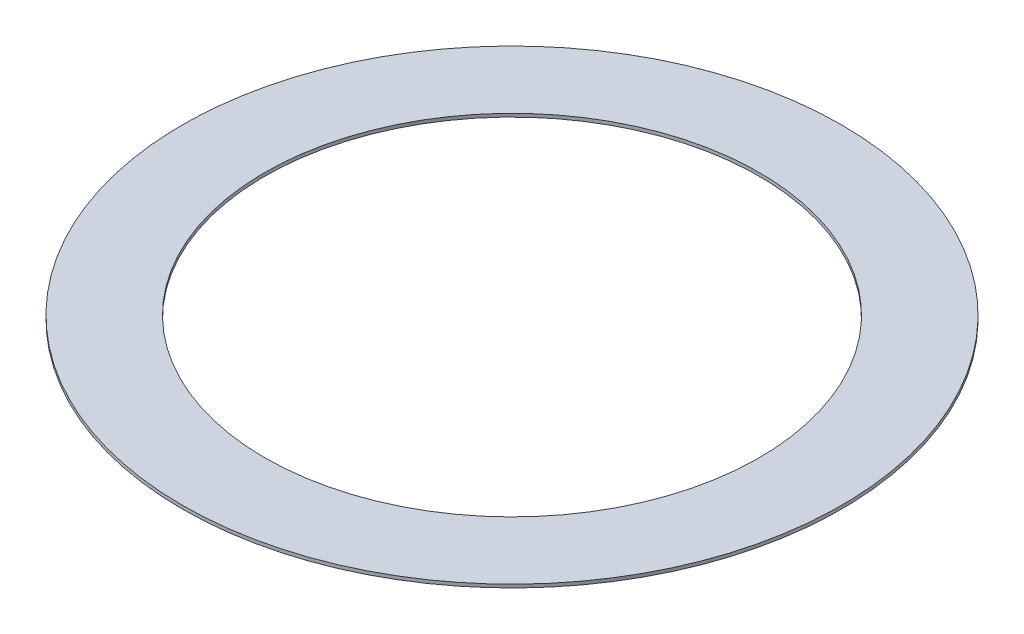
SolidWorks part; units mm, degrees
material "Plain Carbon Steel"
ref_plane "Front-Back Midplane" through (0, 0, 0) normal (0, 0, 1) x (1, 0, 0)
ref_plane "Horizontal Midplane" through (0, 0, 0) normal (0, 1, 0) x (1, 0, 0)
ref_plane "Left-Right Midplane" through (0, 0, 0) normal (1, 0, 0) x (0, 0, -1)
ref_axis "Axis1" through (0, 55, 0) along (0, -1, 0)
sketch "Sketch2" plane through (0, 0, 0) normal (0, 0, -1) x (1, 0, 0)
  line L1 (-9.525, 0) -> (-12.7, 0)
  line L2 (-9.525, 0) -> (-9.525, 0.127)
  line L3 (-9.525, 0.127) -> (-12.7, 0.127)
  line L4 (-12.7, 0) -> (-12.7, 0.127)
  dimension "D1" = 0.127
  dimension "D2" = 9.525
  dimension "D3" = 12.7
revolve "Revolve1" add sketch "Sketch2" angle 360 about axis through (0, 55, 0) along (0, -1, 0)
